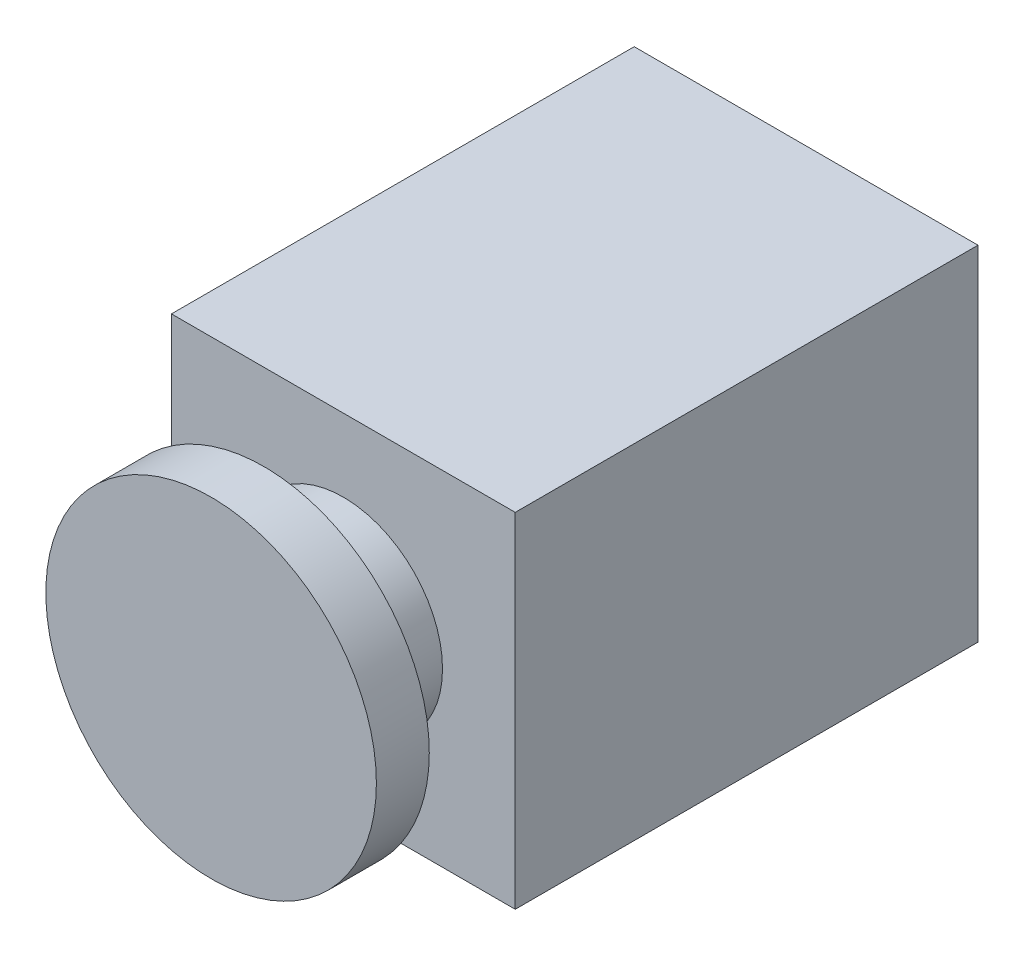
SolidWorks part; units mm, degrees
ref_plane "Front Plane" through (0, 0, 0) normal (0, 0, 1) x (1, 0, 0)
ref_plane "Top Plane" through (0, 0, 0) normal (0, 1, 0) x (1, 0, 0)
ref_plane "Right Plane" through (0, 0, 0) normal (1, 0, 0) x (0, 0, -1)
sketch "Sketch2" plane through (0, 0, 0) normal (0, 0, 1) x (1, 0, 0)
  line L1 (-26, -26) -> (26, -26)
  line L2 (-26, -26) -> (-26, 26)
  line L3 (-26, 26) -> (26, 26)
  line L4 (26, -26) -> (26, 26)
  line L5 (-26, -26) -> (26, 26) construction
  line L6 (-26, 26) -> (26, -26) construction
  point P0 (0, 0)
  dimension "D1" = 52
  dimension "D2" = 52
extrude "Boss-Extrude1" add sketch "Sketch2" along normal blind 70
sketch "Sketch3" plane through (0, 0, 70) normal (0, 0, 1) x (1, 0, 0)
  circle A0 centre (0, 0) radius 15
  dimension "D1" = 30
extrude "Boss-Extrude2" add sketch "Sketch3" along normal blind 20 contours A0
sketch "Sketch4" plane through (0, -26, 0) normal (0, -1, 0) x (1, 0, 0)
  line L0 (-26, 70) -> (26, 70) construction
  line L1 (-26, 70) -> (-26, 0) construction
  circle A0 centre (-16.5, 62) radius 1
  circle A1 centre (-16.5, 28.5) radius 1
  circle A2 centre (-1.5, 62) radius 1
  circle A3 centre (-1.5, 28.5) radius 1
  circle A4 centre (-1.5, 7) radius 1
  circle A5 centre (-16.5, 7) radius 1
  dimension "D3" = 2
  dimension "D1" = 8
  dimension "D2" = 9.5
  dimension "D4" = 33.5
  dimension "D5" = 21.5
  dimension "D6" = 15
extrude "Cut-Extrude1" cut sketch "Sketch4" against normal blind 5 contours A0
sketch "Sketch5" plane through (0, 0, 90) normal (0, 0, 1) x (1, 0, 0)
  circle A0 centre (0, 0) radius 25
  dimension "D1" = 50
extrude "Boss-Extrude3" add sketch "Sketch5" against normal blind 8 contours A0
